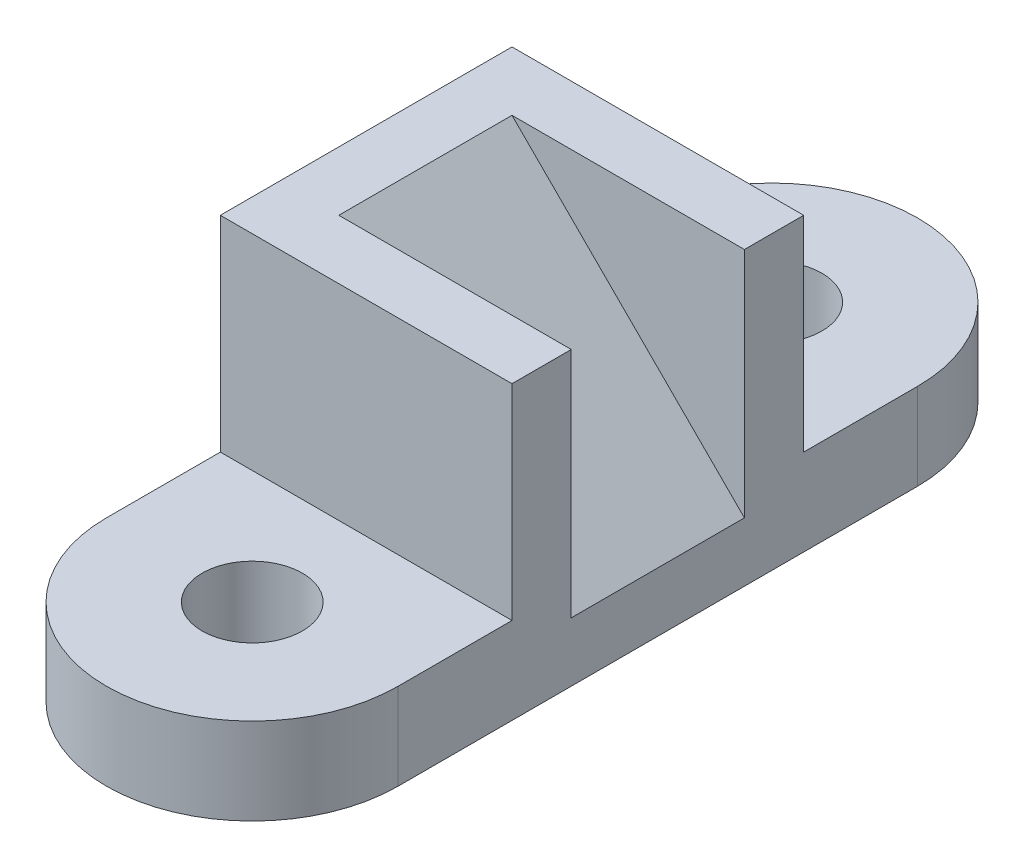
SolidWorks part; units mm, degrees
ref_plane "Ön Düzlem" through (0, 0, 0) normal (0, 0, 1) x (1, 0, 0)
ref_plane "Üst Düzlem" through (0, 0, 0) normal (0, 1, 0) x (1, 0, 0)
ref_plane "Sağ Düzlem" through (0, 0, 0) normal (1, 0, 0) x (0, 0, -1)
sketch "Çizim1" plane through (0, 0, 0) normal (0, 1, 0) x (1, 0, 0)
  line L0 (0, 57) -> (0, -57) construction
  line L1 (32, 57) -> (32, -57)
  line L2 (-32, 57) -> (-32, -57)
  line L3 (0, 0) -> (65.4832, 0) construction
  arc A0 (32, 57) -> (-32, 57) centre (0, 57) ccw
  arc A1 (-32, -57) -> (32, -57) centre (0, -57) ccw
  circle A2 centre (0, -57) radius 11
  circle A3 centre (0, 57) radius 11
  point P2 (0, 0)
  dimension "D2" = 32
  dimension "D3" = 22
  dimension "D1" = 114
extrude "Yükseklik-Ekstrüzyon1" add sketch "Çizim1" along normal blind 19
sketch "Çizim2" plane through (0, 19, 0) normal (0, 1, 0) x (1, 0, 0)
  line L0 (32, -57) -> (32, 57) construction
  line L1 (32, 32) -> (-32, 32)
  line L2 (32, 32) -> (32, 19)
  line L3 (32, 19) -> (-19, 19)
  line L4 (-32, 32) -> (-32, 26.8296)
  line L5 (-32, 57) -> (-32, -57) construction
  line L8 (-32, 26.8296) -> (-32, -32)
  line L9 (-32, -32) -> (-22.4565, -32)
  line L10 (-19, 19) -> (-19, -19)
  line L11 (-22.4565, -32) -> (32, -32)
  line L13 (-19, -19) -> (32, -19)
  line L14 (32, -32) -> (32, -19)
  point P14 (-19, 0)
  dimension "D1" = 64
  dimension "D2" = 13
  dimension "D3" = 13
  dimension "D4" = 13
extrude "Yükseklik-Ekstrüzyon2" add sketch "Çizim2" along normal blind 45
sketch "Çizim3" plane through (0, 19, 0) normal (0, 1, 0) x (1, 0, 0)
  line L0 (32, -19) -> (32, 19) construction
  line L1 (32, -19) -> (-19, -19) construction
  line L2 (-19, -19) -> (-19, 19) construction
  line L3 (-19, 19) -> (32, 19) construction
  line L4 (32, -19) -> (32, 19)
  line L5 (32, -19) -> (-19, -19)
  line L6 (-19, -19) -> (-19, 19)
  line L7 (-19, 19) -> (32, 19)
extrude "Kes-Ekstrüzyon1" cut sketch "Çizim3" against normal blind 6
sketch "Çizim4" plane through (0, 0, -19) normal (0, 0, 1) x (1, 0, 0)
  line L0 (-19, 64) -> (32, 13)
  line L1 (32, 13) -> (-19, 13)
  line L3 (-19, 13) -> (-19, 64)
  point P4 (0, 0)
  point P6 (0, 0)
  point P7 (0, 0)
  point P8 (0, 0)
  point P10 (-19, 22.4234)
  point P11 (0, 0)
extrude "Yükseklik-Ekstrüzyon3" add sketch "Çizim4" along normal up to surface (38 mm away) up to face at (6.5, 38.5, 19)
